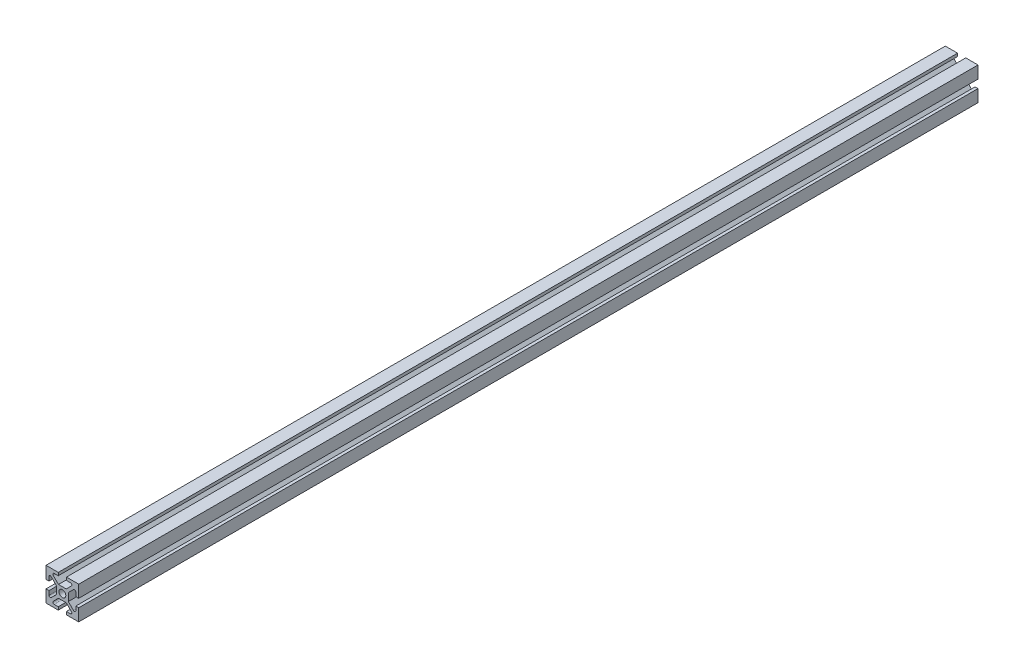
SolidWorks part; units mm, degrees
ref_plane "Alzado" through (0, 0, 0) normal (0, 0, 1) x (1, 0, 0)
ref_plane "Planta" through (0, 0, 0) normal (0, 1, 0) x (1, 0, 0)
ref_plane "Vista lateral" through (0, 0, 0) normal (1, 0, 0) x (0, 0, -1)
sketch "Croquis15" plane through (0, 0, 0) normal (0, 0, 1) x (1, 0, 0)
  line L0 (-10, -10) -> (-10, -2.5)
  line L1 (-10, -10) -> (-2.5, -10)
  line L3 (-10, 10) -> (-2.5, 10)
  line L4 (10, -10) -> (10, -2.5)
  line L5 (-10, 2.5) -> (-10, 10)
  line L6 (10, 2.5) -> (10, 10)
  line L7 (-2.3772, 3.65) -> (2.3772, 3.65)
  line L8 (-3.65, 2.3772) -> (-3.65, -2.3772)
  line L9 (-2.3772, -3.65) -> (2.3772, -3.65)
  line L10 (3.65, 2.3772) -> (3.65, -2.3772)
  line L15 (10, -10) -> (2.5, -10)
  line L16 (10, 10) -> (2.5, 10)
  line L18 (-10, 2.5) -> (-8.2, 2.5)
  line L19 (-10, -2.5) -> (-8.2, -2.5)
  line L20 (-2.5, -10) -> (-2.5, -8.2)
  line L21 (2.5, -10) -> (2.5, -8.2)
  line L22 (-2.5, 10) -> (-2.5, 8.2)
  line L23 (2.5, 10) -> (2.5, 8.2)
  line L24 (-8.2, 2.5) -> (-8.2, 4.9958)
  line L25 (-4.9958, 8.2) -> (-2.5, 8.2)
  line L26 (-8.2, -2.5) -> (-8.2, -4.9958)
  line L27 (-4.9958, -8.2) -> (-2.5, -8.2)
  line L28 (2.5, -8.2) -> (4.9958, -8.2)
  line L29 (2.5, 8.2) -> (4.9958, 8.2)
  line L30 (-6.8343, 5.5615) -> (-3.65, 2.3772)
  line L31 (-5.5615, 6.8343) -> (-2.3772, 3.65)
  line L32 (-3.65, -2.3772) -> (-6.8343, -5.5615)
  line L33 (-2.3772, -3.65) -> (-5.5615, -6.8343)
  line L34 (8.2, -4.9958) -> (8.2, -2.5)
  line L35 (8.2, 4.9958) -> (8.2, 2.5)
  line L36 (8.2, 2.5) -> (10, 2.5)
  line L37 (8.2, -2.5) -> (10, -2.5)
  line L38 (2.3772, -3.65) -> (5.5615, -6.8343)
  line L39 (3.65, -2.3772) -> (6.8343, -5.5615)
  line L40 (2.3772, 3.65) -> (5.5615, 6.8343)
  line L41 (3.65, 2.3772) -> (6.8343, 5.5615)
  circle A0 centre (0, 0) radius 2.1
  arc A1 (-8.2, -4.9958) -> (-6.8343, -5.5615) centre (-7.4, -4.9958) ccw
  arc A2 (-4.9958, -8.2) -> (-5.5615, -6.8343) centre (-4.9958, -7.4) cw
  arc A3 (5.5615, -6.8343) -> (4.9958, -8.2) centre (4.9958, -7.4) cw
  arc A4 (6.8343, -5.5615) -> (8.2, -4.9958) centre (7.4, -4.9958) ccw
  arc A5 (8.2, 4.9958) -> (6.8343, 5.5615) centre (7.4, 4.9958) ccw
  arc A6 (5.5615, 6.8343) -> (4.9958, 8.2) centre (4.9958, 7.4) ccw
  arc A7 (-5.5615, 6.8343) -> (-4.9958, 8.2) centre (-4.9958, 7.4) cw
  arc A8 (-6.8343, 5.5615) -> (-8.2, 4.9958) centre (-7.4, 4.9958) ccw
  point P0 (0, 0)
  dimension "D3" = 0.8
  dimension "D4" = 4.2
  dimension "D1" = 20
  dimension "D2" = 20
  dimension "D5" = 7.5
  dimension "D6" = 7.5
  dimension "D7" = 7.5
  dimension "D8" = 7.5
  dimension "D9" = 7.5
  dimension "D10" = 7.5
  dimension "D11" = 1.8
  dimension "D12" = 1.8
  dimension "D13" = 1.8
  dimension "D15" = 1.8
  dimension "D18" = 1.8
extrude "Saliente-Extruir2" add sketch "Croquis15" against normal blind 550 contours A0 | A1 L32 L8 L30 A8 L24 L18 L5 L3 L22 L25 A7 L31 L7 L40 A6 L29 L23 L16 L6 L36 L35 A5 L41 L10 L39 A4 L34 L37 L4 L15 L21 L28 A3 L38 L9 L33 A2 L27 L20 L1 L0 L19 L26
